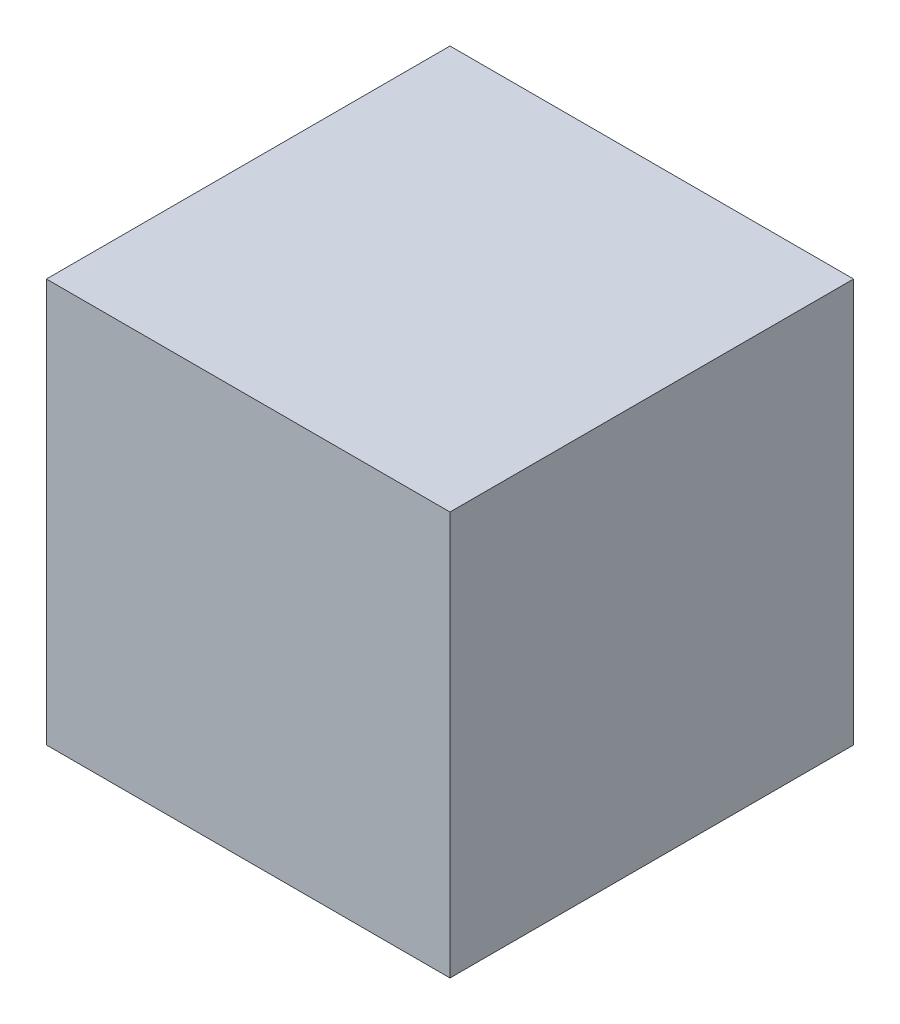
SolidWorks part; units mm, degrees
ref_plane "Front Plane" through (0, 0, 0) normal (0, 0, 1) x (1, 0, 0)
ref_plane "Top Plane" through (0, 0, 0) normal (0, 1, 0) x (1, 0, 0)
ref_plane "Right Plane" through (0, 0, 0) normal (1, 0, 0) x (0, 0, -1)
sketch "Sketch1" plane through (0, 0, 0) normal (0, 1, 0) x (1, 0, 0)
  line L1 (0, 0) -> (12.7, 0)
  line L2 (0, 0) -> (0, 12.7)
  line L3 (0, 12.7) -> (12.7, 12.7)
  line L4 (12.7, 0) -> (12.7, 12.7)
  dimension "D1" = 12.7
  dimension "D2" = 12.7
extrude "Boss-Extrude1" add sketch "Sketch1" along normal blind 12.7 contours L3 L4 L1 L2
